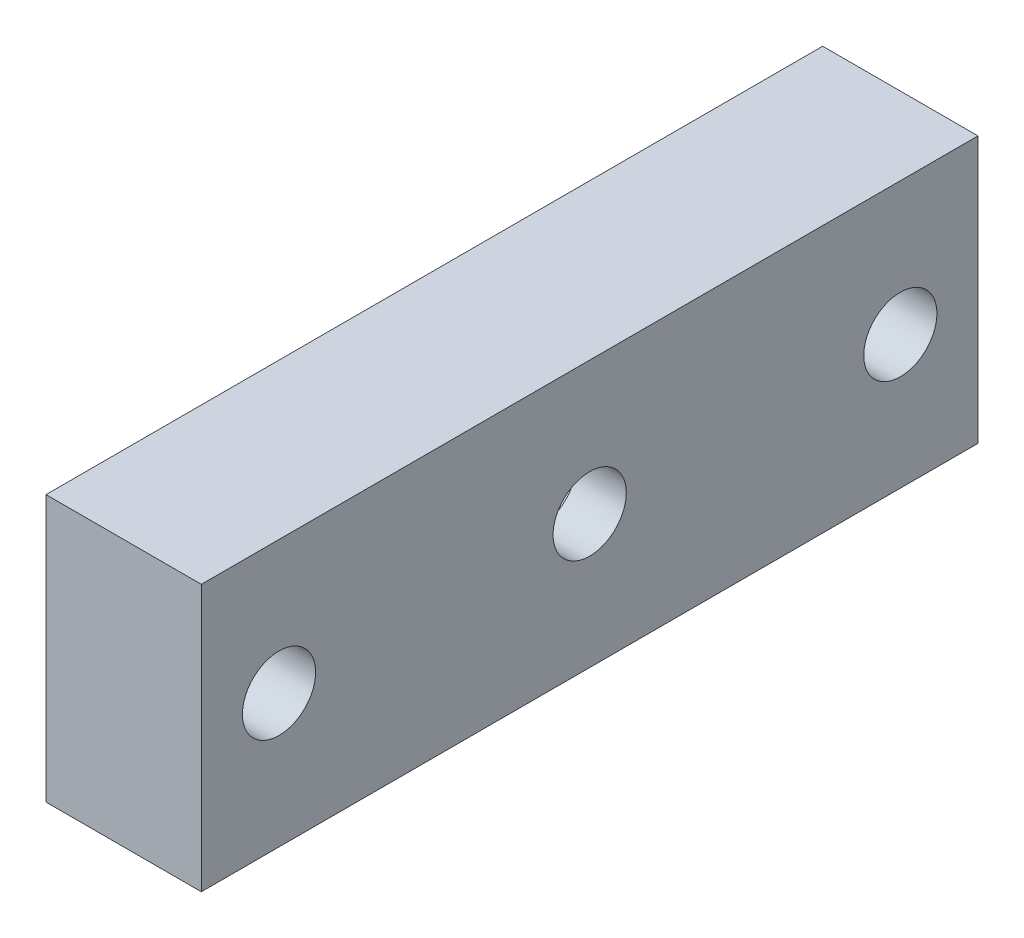
SolidWorks part; units mm, degrees
ref_plane "Front Plane" through (0, 0, 0) normal (0, 0, 1) x (1, 0, 0)
ref_plane "Top Plane" through (0, 0, 0) normal (0, 1, 0) x (1, 0, 0)
ref_plane "Right Plane" through (0, 0, 0) normal (1, 0, 0) x (0, 0, -1)
sketch "Sketch1" plane through (0, 0, 0) normal (1, 0, 0) x (0, 0, -1)
  line L0 (0, 6) -> (3.5, 6) construction
  line L1 (0, 0) -> (35, 0)
  line L2 (0, 0) -> (0, 12)
  line L3 (0, 12) -> (35, 12)
  line L4 (35, 0) -> (35, 12)
  line L5 (31.5, 6) -> (35, 6) construction
  circle A0 centre (3.5, 6) radius 1.65
  circle A1 centre (31.5, 6) radius 1.65
  circle A2 centre (17.5, 6) radius 1.65
  dimension "D3" = 3.3
  dimension "D4" = 6
  dimension "D5" = 6
  dimension "D6" = 28
  dimension "D7" = 3.5
  dimension "D8" = 3.3
  dimension "D9" = 17.5
  dimension "D10" = 6
  dimension "D1" = 12
  dimension "D2" = 35
extrude "Boss-Extrude1" add sketch "Sketch1" along normal blind 7
sketch "Sketch2" plane through (7, 0, 0) normal (1, 0, 0) x (0, 0, -1)
  line L1 (20.7909, 6) -> (19.1454, 8.85)
  line L2 (19.1454, 8.85) -> (15.8546, 8.85)
  line L3 (15.8546, 8.85) -> (14.2091, 6)
  line L4 (14.2091, 6) -> (15.8546, 3.15)
  line L5 (15.8546, 3.15) -> (19.1454, 3.15)
  line L6 (19.1454, 3.15) -> (20.7909, 6)
  circle A0 centre (17.5, 6) radius 2.85 construction
  dimension "D1" = 5.7
extrude "Cut-Extrude1" cut sketch "Sketch2" against normal blind 2.5 from offset 2.25
